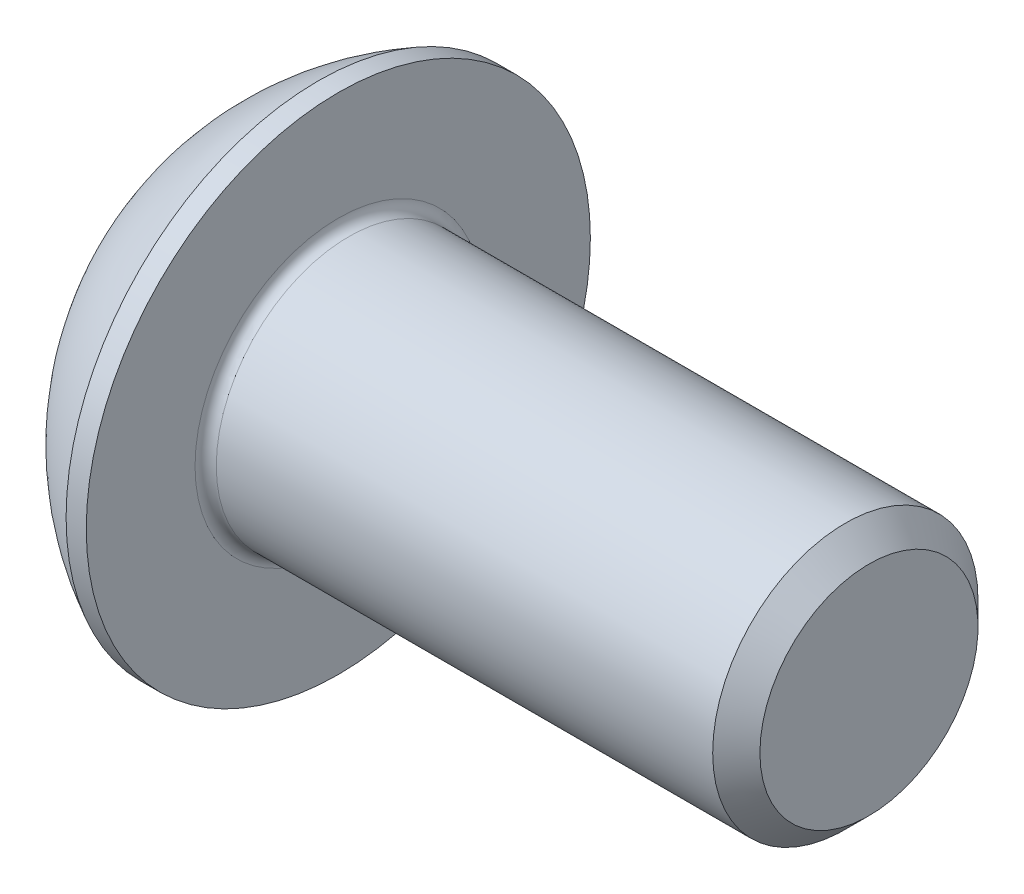
SolidWorks part; units mm, degrees
ref_plane "Plane1" through (0, 0, 0) normal (0, 0, 1) x (1, 0, 0)
ref_plane "Plane2" through (0, 0, 0) normal (0, 1, 0) x (1, 0, 0)
ref_plane "Plane3" through (0, 0, 0) normal (1, 0, 0) x (0, 0, -1)
sketch "BodySke" plane through (0, 0, 0) normal (0, 0, 1) x (1, 0, 0)
  line L0 (12.75, 0) -> (12.75, 2.055)
  line L1 (12.305, 2.5) -> (2.75, 2.5)
  line L2 (2.75, 2.5) -> (2.75, 4.75)
  line L3 (2.75, 4.75) -> (2.37, 4.75)
  line L4 (0, 0) -> (101.6, 0) construction
  line L5 (2.75, -4.75) -> (2.37, -4.75) construction
  line L6 (55.6768, -2.5) -> (2.75, -2.5) construction
  line L7 (12.75, 0) -> (0, 0)
  line L8 (0, 2.375) -> (0, -2.375) construction
  line L9 (0, 0) -> (0, 2.375)
  line L10 (12.75, 2.055) -> (12.305, 2.5)
  line L11 (12.75, -2.055) -> (12.305, -2.5) construction
  line L12 (3.55, 9.525) -> (3.55, -2.5) construction
  line L13 (2.75, 9.525) -> (2.75, -2.5) construction
  arc A1 (0, 2.375) -> (2.37, 4.75) centre (4.755, 0) cw
  dimension "D1" = 4.75
  dimension "Diameter" = 5
  dimension "Length" = 10
  dimension "Head_dia" = 9.5
  dimension "Head_ht" = 2.75
  dimension "Head_side_ht" = 0.38
  dimension "Minor_dia" = 4.11
  dimension "Body_ch_ang" = 45
  dimension "Advance" = 0.8
  dimension "Thread_nom" = 10
revolve "BaseBody" add sketch "BodySke" angle 360 about L4
cosmetic thread "ThreadCosmetic" parameters "Thread_length"=8.4, "Thread_minor"=4.11
fillet "Fillet1" radius 0.2 1 edges at (2.75, 0, 2.5)
sketch "Sketch2" plane through (0, 0, 0) normal (0, 0, 1) x (1, 0, 0)
  line L0 (0, 1.5) -> (1.56, 1.5)
  line L1 (1.56, 1.5) -> (2.426, 0)
  line L3 (2.426, 0) -> (0, 0)
  line L4 (0, 0) -> (0, 1.5)
  line L5 (0, -1.5) -> (1.56, -1.5) construction
  line L6 (0, 0) -> (47.625, 0) construction
  dimension "D2" = 60
  dimension "PreBroach_depth" = 1.56
  dimension "PreBroach_dia" = 3
revolve "PreBroach" cut sketch "Sketch2" angle 360 about L6
sketch "Sketch3" plane through (0, 0, 0) normal (1, 0, 0) x (0, 0, -1)
  line L0 (-1.5, -0.866) -> (-1.5, 0.866)
  line L1 (-1.5, 0.866) -> (0, 1.7321)
  line L2 (0, 1.7321) -> (1.5, 0.866)
  line L3 (1.5, 0.866) -> (1.5, -0.866)
  line L4 (1.5, -0.866) -> (0, -1.7321)
  line L5 (0, -1.7321) -> (-1.5, -0.866)
  dimension "D1" = 1.5
  dimension "D2" = 1.5
  dimension "D3" = 3
  dimension "Hex_size" = 3
extrude "Hex" cut sketch "Sketch3" along normal blind 1.56
sketch "ThdSchSke" plane through (0, 0, 0) normal (0, 0, 1) x (1, 0, 0)
  line L0 (4.35, -2.055) -> (4.0384, -2.5)
  line L1 (4.35, -2.055) -> (4.6616, -2.5)
  line L2 (4.6616, -2.5) -> (4.6616, -3.125)
  line L3 (-3.175, 0) -> (5.1513, 0) construction
  line L5 (4.6616, -3.125) -> (4.0384, -3.125)
  line L6 (4.0384, -3.125) -> (4.0384, -2.5)
  dimension "Thread_minor" = 4.11
  dimension "Diameter" = 5
  dimension "Start" = 4.35
  dimension "SideAngle" = 55
  dimension "VeeAngle" = 70
  dimension "Overcut" = 6.25
revolve "ThreadSchematic" [suppressed] cut sketch "ThdSchSke" angle 360 about L3
pattern_linear "ThdSchPat" [suppressed]
equation "\"D1@BodySke\" = \"Head_dia@BodySke\" * .5"
equation "\"Thread_minor@ThreadCosmetic\" = \"Minor_dia@BodySke\""
equation "\"D1@Sketch3\" = \"Hex_size@Sketch3\" / 2"
equation "\"D2@Sketch3\" = \"D1@Sketch3\""
equation "\"D3@Sketch3\" = \"Hex_size@Sketch3\""
equation "\"Thread_length@ThreadCosmetic\" = ((sgn( (\"Length@BodySke\" - \"Advance@BodySke\" * 2.0) - \"Thread_nom@BodySke\" )-1)*( (\"Length@BodySke\" - \"Advance@BodySke\" * 2.0) - \"Thread_nom@BodySke\" ))/-2+ \"Thread_nom@BodySke\""
equation "\"Thread_minor@ThdSchSke\" = \"Minor_dia@BodySke\""
equation "\"Diameter@ThdSchSke\" = \"Diameter@BodySke\""
equation "\"Overcut@ThdSchSke\" = \"Diameter@BodySke\" * 1.25"
equation "\"Start@ThdSchSke\" = \"Head_ht@BodySke\" + \"Length@BodySke\" - \"Thread_length@ThreadCosmetic\"  '---Non-countersunk---"
equation "\"Num_threads@ThdSchPat\" = int( \"Thread_length@ThreadCosmetic\" / \"Advance@BodySke\" + 0.999 )  + 1"
equation "\"Advance@ThdSchPat\" = \"Thread_length@ThreadCosmetic\" /  (\"Num_threads@ThdSchPat\" - 1) 'relax it"
equation "\"Num_threads@ThdSchPat\" = \"Num_threads@ThdSchPat\" - sgn( \"Num_threads@ThdSchPat\" - 1) '---chamfered tips only---"
